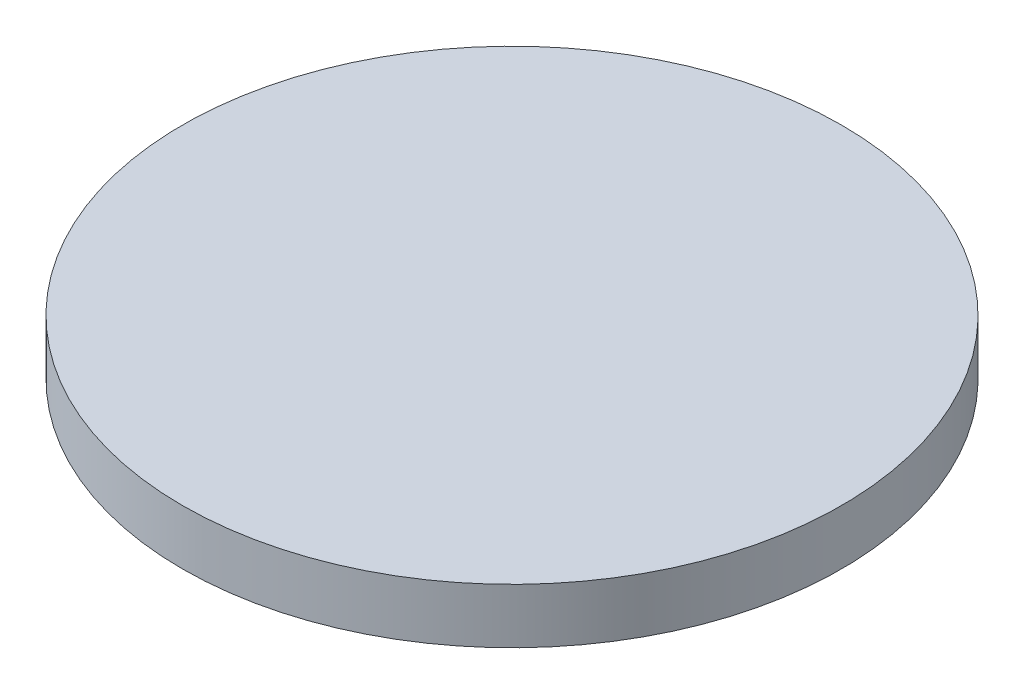
SolidWorks part; units mm, degrees
ref_plane "Front Plane" through (0, 0, 0) normal (0, 0, 1) x (1, 0, 0)
ref_plane "Top Plane" through (0, 0, 0) normal (0, 1, 0) x (1, 0, 0)
ref_plane "Right Plane" through (0, 0, 0) normal (1, 0, 0) x (0, 0, -1)
sketch "Sketch1" plane through (0, 0, 0) normal (0, 1, 0) x (1, 0, 0)
  circle A0 centre (0, 0) radius 3000
extrude "Boss-Extrude1" add sketch "Sketch1" along normal blind 500
